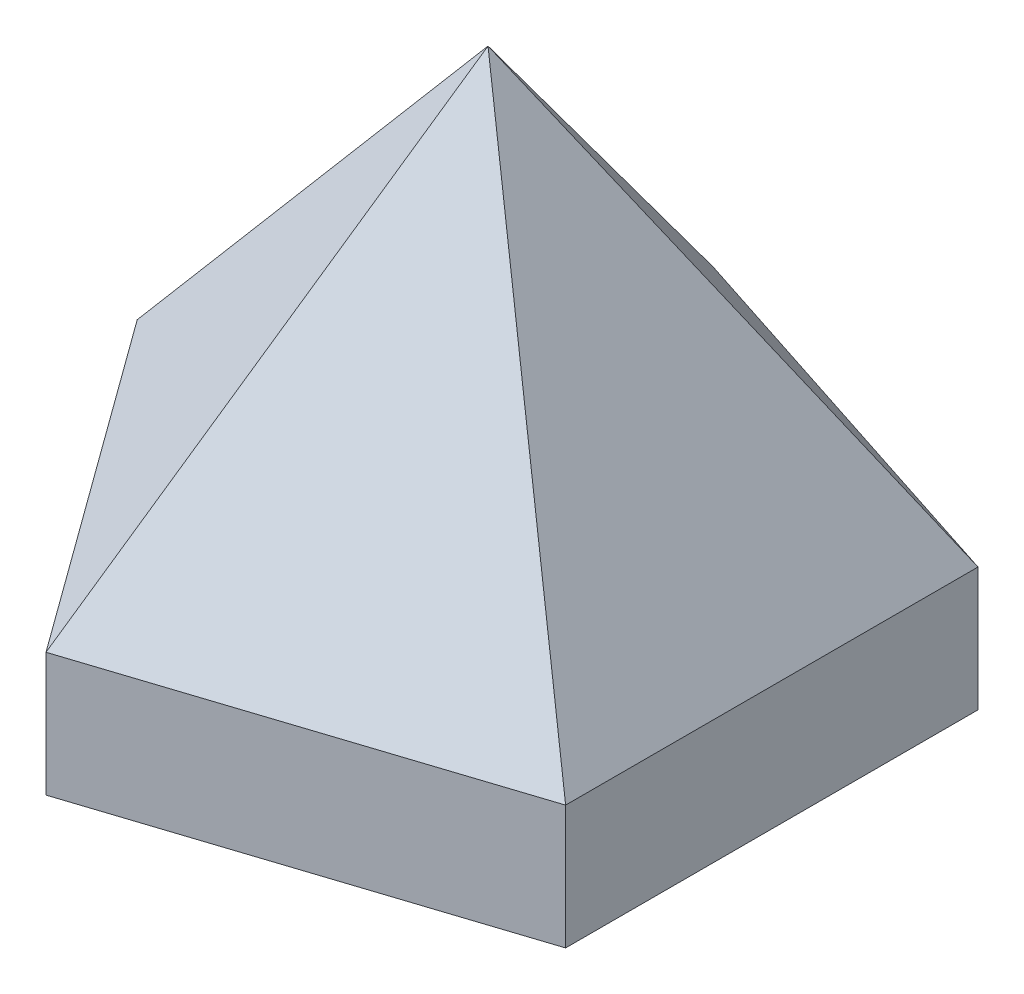
SolidWorks part; units mm, degrees
ref_plane "Front Plane" through (0, 0, 0) normal (0, 0, 1) x (1, 0, 0)
ref_plane "Top Plane" through (0, 0, 0) normal (0, 1, 0) x (1, 0, 0)
ref_plane "Right Plane" through (0, 0, 0) normal (1, 0, 0) x (0, 0, -1)
sketch "Sketch1" plane through (0, 0, 0) normal (0, 1, 0) x (1, 0, 0)
  line L0 (0, 0) -> (78.5644, 0) construction
  line L2 (69.3893, -95.4508) -> (116.9421, -80)
  line L3 (116.9421, -80) -> (116.9421, -30)
  line L4 (116.9421, -30) -> (69.3893, -14.5492)
  line L5 (69.3893, -14.5492) -> (40, -55)
  line L6 (40, -55) -> (69.3893, -95.4508)
  circle A0 centre (82.5325, -55) radius 34.4095 construction
  dimension "D1" = 50
  dimension "D2" = 30
  dimension "D3" = 40
extrude "Extrude1" add sketch "Sketch1" along normal blind 15
ref_plane "Plane1" through (0, 65, 0) normal (0, 1, 0) x (-1, 0, 0)
sketch "Sketch2" plane through (0, 65, 0) normal (0, 1, 0) x (-1, 0, 0)
  line L0 (-40, 55) -> (-116.9421, 55) construction
  line L1 (-116.9421, 80) -> (-116.9421, 30) construction
  line L2 (-69.3893, 95.4508) -> (-93.1657, 22.2746) construction
  line L3 (-116.9421, 30) -> (-69.3893, 14.5492) construction
  point P10 (-82.5325, 55)
sketch "Sketch3" plane through (0, 15, 0) normal (0, 1, 0) x (1, 0, 0)
  line L0 (69.3893, -95.4508) -> (40, -55)
  line L1 (40, -55) -> (69.3893, -14.5492)
  line L2 (69.3893, -14.5492) -> (116.9421, -30)
  line L3 (116.9421, -30) -> (116.9421, -80)
  line L4 (116.9421, -80) -> (69.3893, -95.4508)
loft "Loft1" add profiles "Sketch3", "Sketch2"
sketch "Sketch4" plane through (0, 0, 0) normal (0, 1, 0) x (1, 0, 0)
  line L0 (0, 0) -> (76.9749, -133.3245)
  line L1 (0, 0) -> (101.78, 0) construction
  dimension "D1" = 60
sketch "Sketch5" plane through (0, 0, 0) normal (0, 0, 1) x (1, 0, 0)
  line L0 (0, 0) -> (94.8216, 74.6785)
ref_plane "Section Plane" through (0, 0, 0) normal (-0.5827, 0.7398, 0.3364) x (-0.8127, -0.5304, -0.2412)
